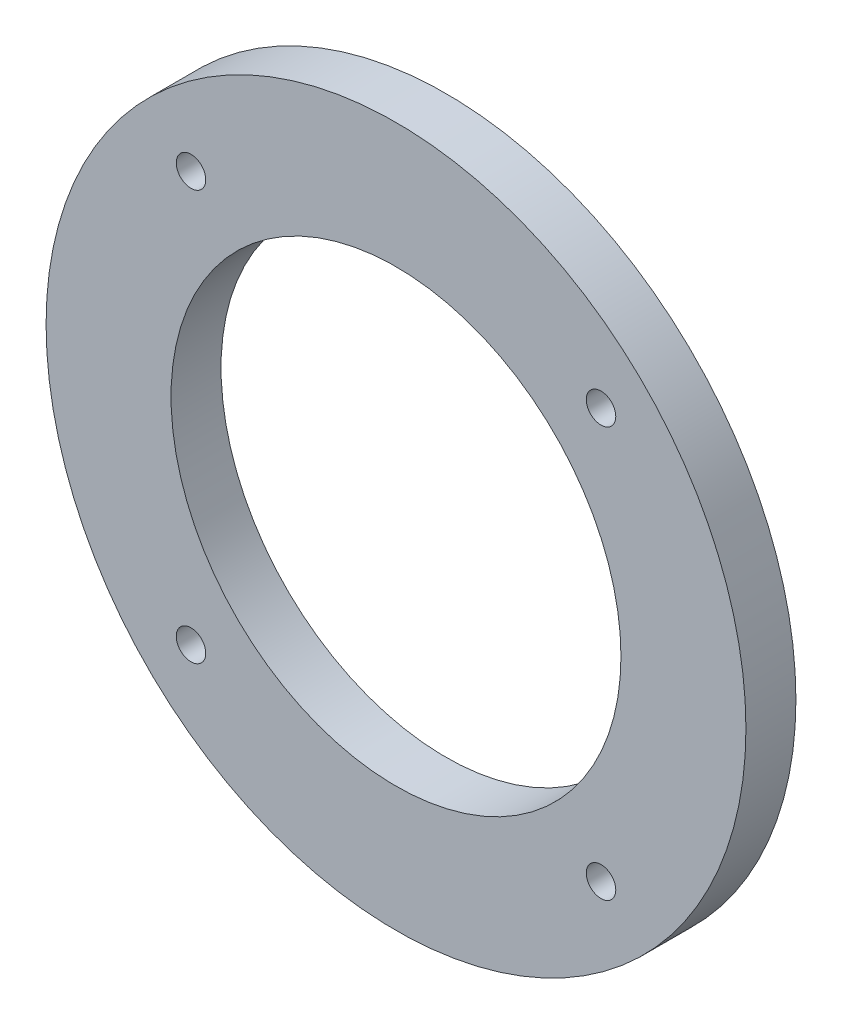
SolidWorks part; units mm, degrees
ref_plane "Front Plane" through (0, 0, 0) normal (0, 0, 1) x (1, 0, 0)
ref_plane "Top Plane" through (0, 0, 0) normal (0, 1, 0) x (1, 0, 0)
ref_plane "Right Plane" through (0, 0, 0) normal (1, 0, 0) x (0, 0, -1)
sketch "Sketch1" plane through (0, 0, 0) normal (0, 0, 1) x (1, 0, 0)
  line L0 (0, 0) -> (0, 35) construction
  line L1 (0, 0) -> (-35, 0) construction
  line L2 (0, 0) -> (-24.7487, 24.7487) construction
  circle A0 centre (0, 0) radius 35
  circle A1 centre (0, 0) radius 22.5
  circle A2 centre (-20.5061, 20.5061) radius 1.475
  circle A4 centre (20.5061, 20.5061) radius 1.475
  circle A5 centre (20.5061, -20.5061) radius 1.475
  circle A6 centre (-20.5061, -20.5061) radius 1.475
  point P18 (0, 0)
  dimension "D1" = 70
  dimension "D2" = 45
  dimension "D3" = 2.95
  dimension "D5" = 45
  dimension "D4" = 29
  dimension "D6" = 4
extrude "Boss-Extrude1" add sketch "Sketch1" along normal blind 5
